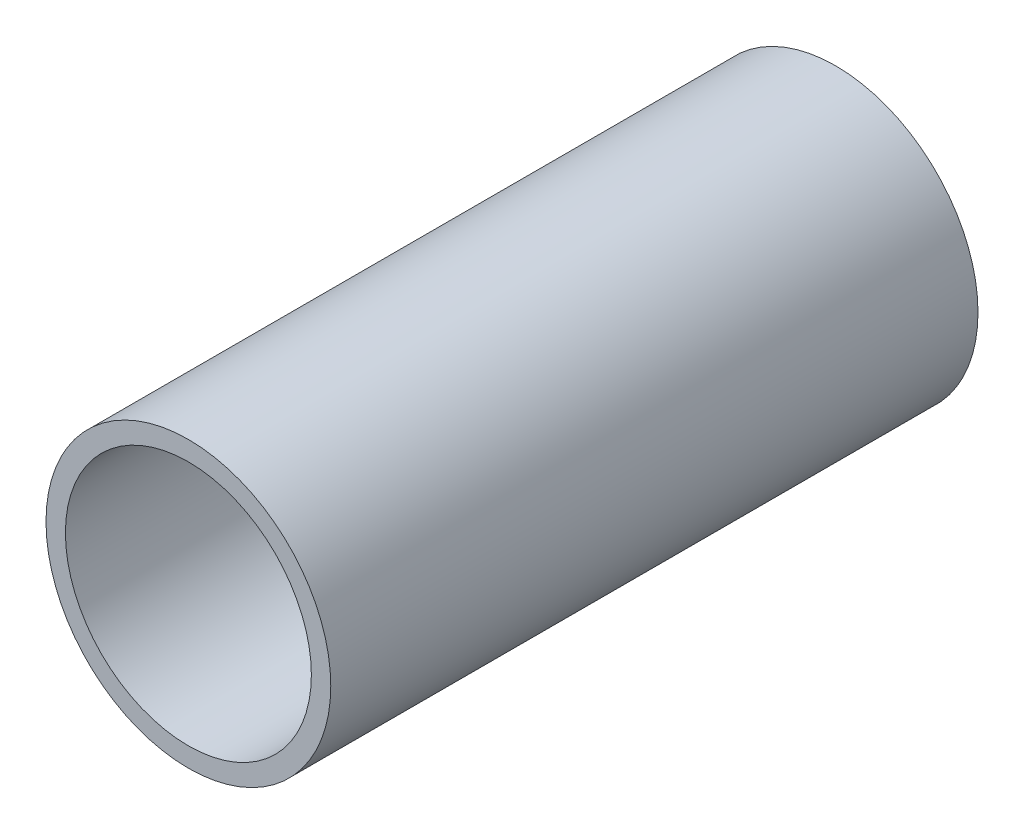
SolidWorks part; units mm, degrees
ref_plane "Front Plane" through (0, 0, 0) normal (0, 0, 1) x (1, 0, 0)
ref_plane "Top Plane" through (0, 0, 0) normal (0, 1, 0) x (1, 0, 0)
ref_plane "Right Plane" through (0, 0, 0) normal (1, 0, 0) x (0, 0, -1)
sketch "Sketch1" plane through (0, 0, 0) normal (0, 0, 1) x (1, 0, 0)
  circle A0 centre (0, 0) radius 22
  circle A1 centre (0, 0) radius 19
extrude "Boss-Extrude1" add sketch "Sketch1" along normal blind 100
